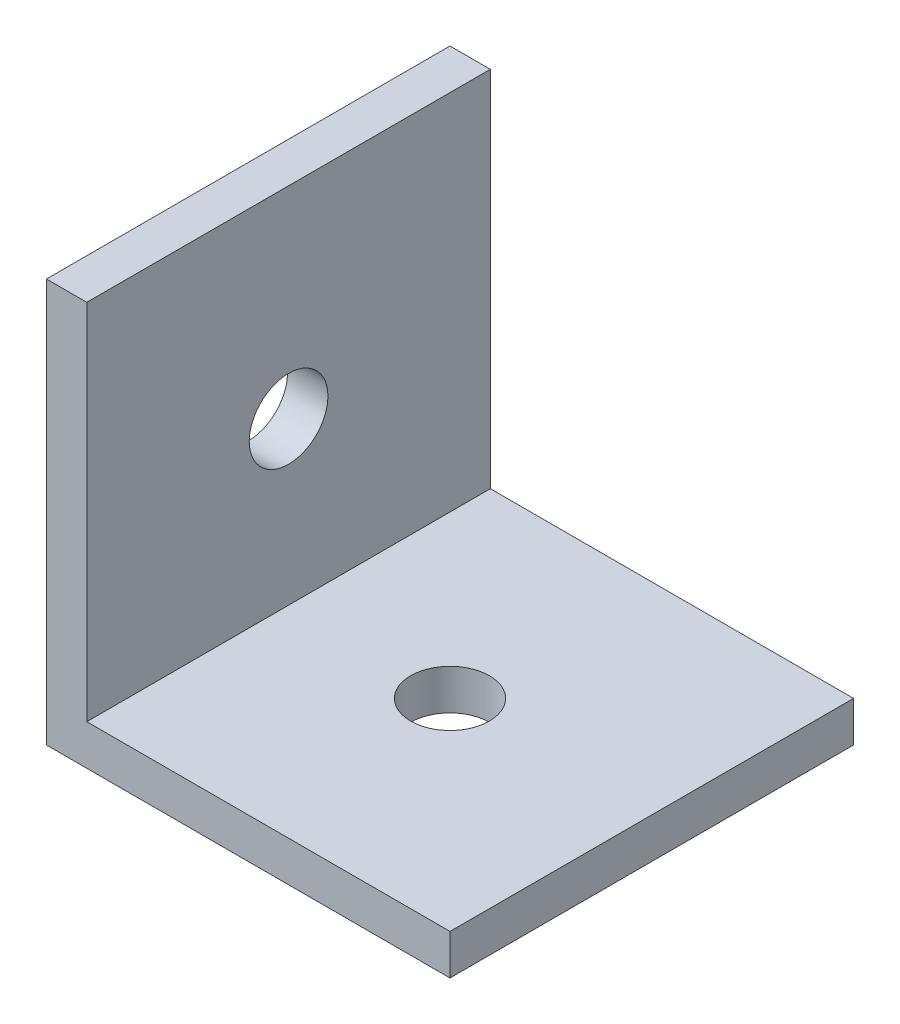
SolidWorks part; units mm, degrees
ref_plane "Front Plane" through (0, 0, 0) normal (0, 0, 1) x (1, 0, 0)
ref_plane "Top Plane" through (0, 0, 0) normal (0, 1, 0) x (1, 0, 0)
ref_plane "Right Plane" through (0, 0, 0) normal (1, 0, 0) x (0, 0, -1)
sketch "Sketch1" plane through (0, 0, 0) normal (0, 0, 1) x (1, 0, 0)
  line L0 (0, 0) -> (0, 25.4)
  line L1 (0, 0) -> (25.4, 0)
  dimension "D1" = 25.4
extrude "Extrude-Thin1" add sketch "Sketch1" along normal blind 25.4 thin
sketch "Sketch3" plane through (0, 0, 0) normal (-1, 0, 0) x (0, 0, 1)
  line L0 (12.7, 0) -> (12.7, 25.4) construction
  line L1 (25.4, 0) -> (0, 0) construction
  line L2 (25.4, 25.4) -> (0, 25.4) construction
  circle A0 centre (12.7, 12.7) radius 2.4765
  dimension "D2" = 4.953
  dimension "D1" = 12.7
extrude "Cut-Extrude1" cut sketch "Sketch3" against normal through all
sketch "Sketch4" plane through (0, 0, 0) normal (0, -1, 0) x (1, 0, 0)
  line L0 (25.4, 12.7) -> (0, 12.7) construction
  line L1 (25.4, 25.4) -> (25.4, 0) construction
  line L2 (0, 25.4) -> (0, 0) construction
  circle A0 centre (12.7, 12.7) radius 2.4765
  dimension "D2" = 4.953
  dimension "D1" = 12.7
extrude "Cut-Extrude2" cut sketch "Sketch4" against normal through all
